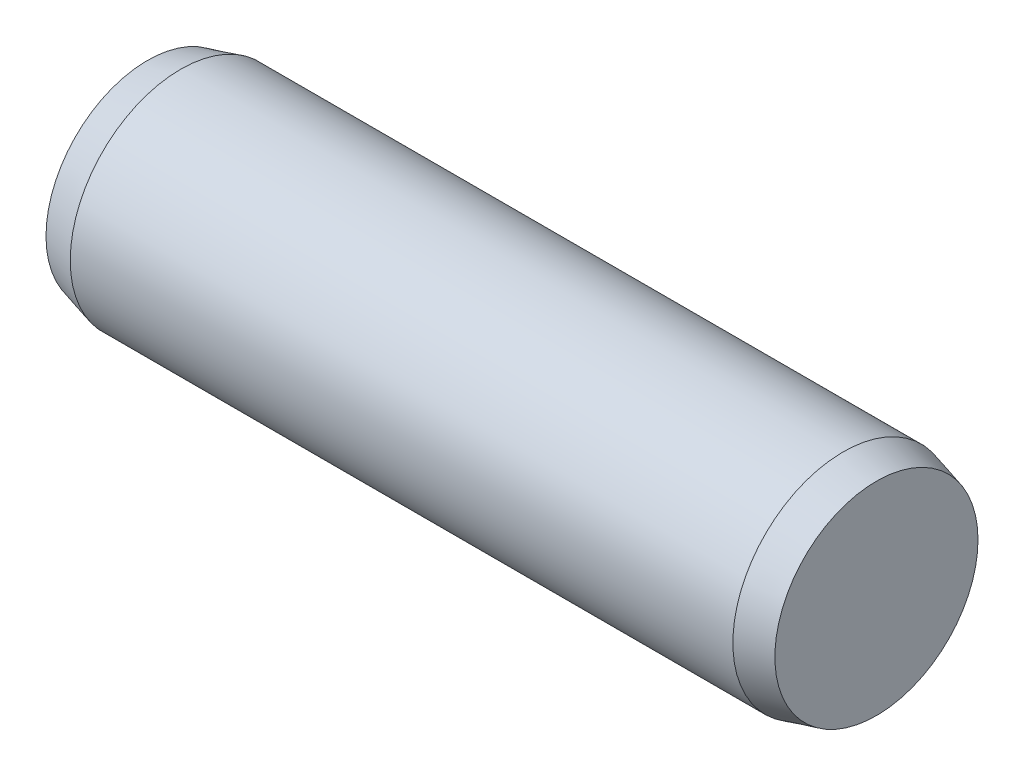
SolidWorks part; units mm, degrees
ref_plane "Front Plane" through (0, 0, 0) normal (0, 0, 1) x (1, 0, 0)
ref_plane "Top Plane" through (0, 0, 0) normal (0, 1, 0) x (1, 0, 0)
ref_plane "Right Plane" through (0, 0, 0) normal (1, 0, 0) x (0, 0, -1)
sketch "Sketch1" plane through (0, 0, 0) normal (0, 0, 1) x (1, 0, 0)
  line L0 (-3, 0) -> (3, 0) construction
  line L1 (3, 1) -> (3, -1) construction
  line L2 (-3, 1) -> (-3, -1) construction
  line L3 (3.3, 1) -> (3.3, -1) construction
  line L4 (-3.3, 1) -> (-3.3, -1) construction
  line L5 (-3, 0) -> (-3.3, 0) construction
  line L6 (3, 0) -> (3.3, 0) construction
  dimension "D1" = 0.3
  dimension "Dia" = 2
  dimension "Length" = 6
  dimension "C" = 0.3
sketch "Sketch2" plane through (0, 0, 0) normal (1, 0, 0) x (0, 0, -1)
  circle A0 centre (0, 0) radius 1
extrude "Extrude1" add sketch "Sketch2" against normal up to vertex (3 mm away) and the other way up to vertex (3 mm away) up to point (-3, 1, 0) other way up to point (3, 1, 0)
sketch "Sketch3" plane through (3, 0, 0) normal (1, 0, 0) x (0, 0, -1)
  circle A1 centre (0, 0) radius 1
  circle A2 centre (0, 0) radius 1
  dimension "D1" = 0
extrude "Extrude2" add sketch "Sketch3" along normal up to vertex (0.3 mm away) draft 15 up to point (3.3, 0, 0)
sketch "Sketch4" plane through (-3, 0, 0) normal (-1, 0, 0) x (0, 0, 1)
  circle A1 centre (0, 0) radius 1
  circle A2 centre (0, 0) radius 1
  dimension "D1" = 0
extrude "Extrude3" add sketch "Sketch4" along normal up to vertex (0.3 mm away) draft 15 up to point (-3.3, 0, 0)
equation "\"D1@Sketch1\" = \"C@Sketch1\""
